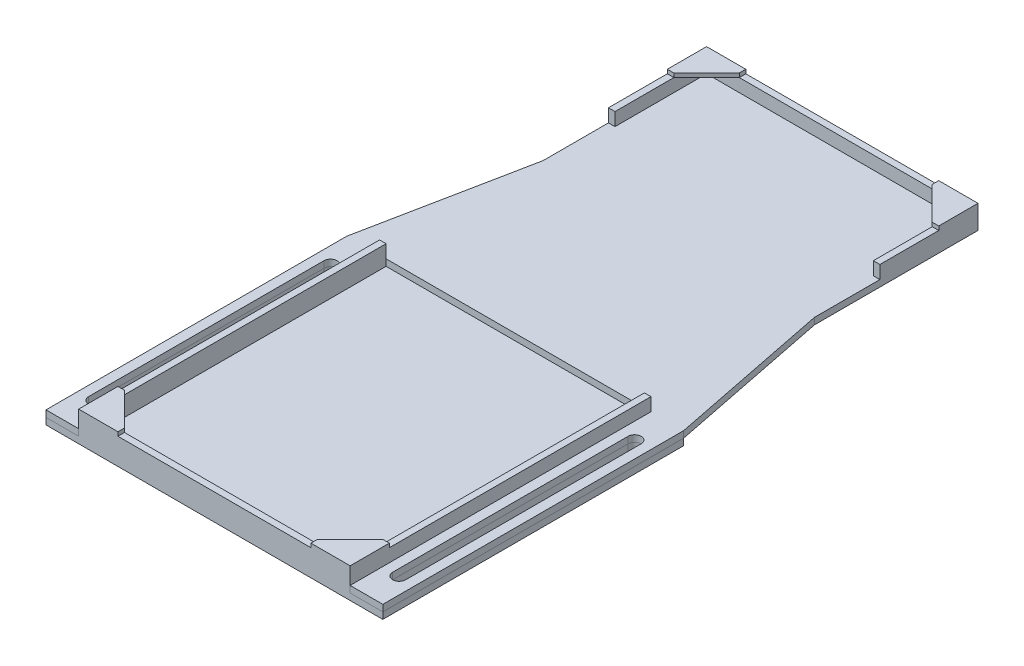
SolidWorks part; units mm, degrees
ref_plane "Alzado" through (0, 0, 0) normal (0, 0, 1) x (1, 0, 0)
ref_plane "Planta" through (0, 0, 0) normal (0, 1, 0) x (1, 0, 0)
ref_plane "Vista lateral" through (0, 0, 0) normal (1, 0, 0) x (0, 0, -1)
sketch "Croquis1" plane through (0, 0, 0) normal (0, 1, 0) x (1, 0, 0)
  line L0 (-2.3216, 1.9) -> (2.3216, 1.9) construction
  line L1 (0, 3) -> (0, -3) construction
  line L2 (3, 0) -> (-3, 0) construction
  line L3 (-2.3216, -1.9) -> (2.3216, -1.9) construction
  line L4 (2.3216, 1.9) -> (-2.3216, 1.9)
  line L5 (2.3216, -1.9) -> (-2.3216, -1.9)
  line L7 (10, -10) -> (-10, -10)
  line L8 (10, -10) -> (10, 10)
  line L9 (10, 10) -> (-10, 10)
  line L10 (-10, -10) -> (-10, 10)
  line L11 (10, -10) -> (-10, 10) construction
  line L12 (10, 10) -> (-10, -10) construction
  circle A0 centre (0, 0) radius 3
  circle A1 centre (0, 0) radius 1.9 construction
  point P11 (0, 1.9)
  dimension "D1" = 6
  dimension "D2" = 3.8
  dimension "D3" = 20
extrude "Saliente-Extruir1" add sketch "Croquis1" along normal blind 5 contours L10 L7 L8 L9 A0 | L5 A0 | L4 A0
sketch "Croquis2" plane through (0, 5, 0) normal (0, 1, 0) x (1, 0, 0)
  line L0 (-39.5, 0) -> (39.5, 0) construction
  line L1 (-10, 10) -> (-39.5, 10)
  line L6 (-39.5, 10) -> (-39.5, 0)
  line L7 (-39.5, 0) -> (-39.5, -80)
  line L8 (-39.5, -80) -> (39.5, -80)
  line L9 (0, 0) -> (0, -80) construction
  line L10 (39.5, 0) -> (39.5, -80)
  line L11 (39.5, 10) -> (39.5, 0)
  line L12 (10, 10) -> (39.5, 10)
  line L13 (-10, 10) -> (10, 10)
  point P0 (0, 0)
  point P4 (0, 0)
  dimension "D1" = 79
  dimension "D2" = 80
extrude "Saliente-Extruir2" add sketch "Croquis2" along normal blind 2
sketch "Croquis3" plane through (0, 5, 0) normal (0, -1, 0) x (1, 0, 0)
  line L0 (39.5, 80) -> (39.5, -10) construction
  line L1 (-39.5, 80) -> (39.5, 80) construction
  line L2 (-39.5, -10) -> (-39.5, 80) construction
  line L3 (39.5, 80) -> (39.5, -10)
  line L4 (-39.5, 80) -> (39.5, 80)
  line L5 (-39.5, -10) -> (-39.5, 80)
  line L11 (-41.5, -10) -> (-41.5, 82)
  line L12 (-41.5, 82) -> (41.5, 82)
  line L13 (41.5, 82) -> (41.5, -10)
  line L14 (-41.5, -10) -> (-39.5, -10)
  line L15 (41.5, -10) -> (39.5, -10)
  dimension "D1" = 2
extrude "Saliente-Extruir3" add sketch "Croquis3" against normal blind 8
sketch "Croquis4" plane through (0, 13, 0) normal (0, 1, 0) x (1, 0, 0)
  line L0 (-29.5, -80) -> (-39.5, -70)
  line L1 (39.5, -70) -> (29.5, -80)
  line L2 (-39.5, -70) -> (-39.5, -80)
  line L3 (-39.5, -80) -> (-29.5, -80)
  line L4 (39.5, -70) -> (39.5, -80)
  line L5 (39.5, -80) -> (29.5, -80)
  line L6 (-39.5, -70) -> (-41.5, -70)
  line L7 (-41.5, -82) -> (-41.5, 10) construction
  line L8 (39.5, -80) -> (-39.5, -80)
  line L9 (-39.5, -80) -> (-39.5, 10)
  line L10 (-39.5, 10) -> (-41.5, 10)
  line L11 (-41.5, 10) -> (-41.5, -82)
  line L12 (-41.5, -82) -> (41.5, -82)
  line L13 (41.5, -82) -> (41.5, 10)
  line L14 (41.5, 10) -> (39.5, 10)
  line L15 (39.5, 10) -> (39.5, -80)
  line L16 (29.5, -80) -> (-29.5, -80)
  line L24 (-29.5, -80) -> (-29.5, -82)
  line L25 (41.5, -82) -> (-41.5, -82) construction
  line L26 (39.5, -70) -> (41.5, -70)
  line L27 (41.5, 10) -> (41.5, -82) construction
  line L28 (29.5, -80) -> (29.5, -82)
  line M9 (39.5, -80) -> (-39.5, -80)
  line M10 (-39.5, -80) -> (-39.5, 10)
  line M12 (-41.5, 10) -> (-41.5, -82)
  line M13 (-41.5, -82) -> (41.5, -82)
  line M14 (41.5, -82) -> (41.5, 10)
  line M16 (39.5, 10) -> (39.5, -80)
  dimension "D1" = 0
extrude "Saliente-Extruir4" add sketch "Croquis4" along normal blind 1.2 contours L0 M9 M10 | L24 L6 M9 M10 M12 M13 | L1 M16 M9 | L28 L26 M9 M13 M14 M16
sketch "Croquis5" plane through (0, 5, 0) normal (0, -1, 0) x (1, 0, 0)
  line L0 (-41.5, 82) -> (-41.5, -10) construction
  line L1 (-41.5, 82) -> (-41.5, -10)
  line L2 (-41.5, 82) -> (-51.5, 82)
  line L3 (-51.5, 82) -> (-51.5, -10)
  line L4 (-51.5, -10) -> (-41.5, -10)
  line L5 (-46.5, 82) -> (-46.5, -10) construction
  line L6 (-46.5, 0) -> (-46.5, 72) construction
  line L7 (-48.5, 0) -> (-48.5, 72)
  line L8 (-44.5, 0) -> (-44.5, 72)
  line L9 (0, 82) -> (0, -10) construction
  line L10 (41.5, 82) -> (-41.5, 82) construction
  line L11 (10, -10) -> (-10, -10) construction
  line L12 (46.5, 0) -> (46.5, 72) construction
  line L13 (48.5, 0) -> (48.5, 72)
  line L14 (44.5, 0) -> (44.5, 72)
  line L15 (41.5, 82) -> (51.5, 82)
  line L16 (41.5, 82) -> (41.5, -10)
  line L17 (51.5, 82) -> (51.5, -10)
  line L18 (51.5, -10) -> (41.5, -10)
  arc A0 (-48.5, 0) -> (-44.5, 0) centre (-46.5, 0) ccw
  arc A1 (-44.5, 72) -> (-48.5, 72) centre (-46.5, 72) ccw
  arc A2 (48.5, 0) -> (44.5, 0) centre (46.5, 0) cw
  arc A3 (44.5, 72) -> (48.5, 72) centre (46.5, 72) cw
  point P6 (-46.5, 0)
  point P9 (-46.5, 36)
  point P22 (46.5, 36)
  dimension "D1" = 10
  dimension "D2" = 10
  dimension "D3" = 10
  dimension "D4" = 4
extrude "Saliente-Extruir5" add sketch "Croquis5" against normal blind 2
sketch "Croquis6" plane through (0, 7, 0) normal (0, 1, 0) x (1, 0, 0)
  line L4 (-48.5, -72) -> (-48.5, 0) construction
  line L5 (-44.5, 0) -> (-44.5, -72) construction
  line L6 (44.5, -72) -> (44.5, 0) construction
  line L7 (48.5, 0) -> (48.5, -72) construction
  line L8 (41.5, 10) -> (41.5, -82)
  line L9 (41.5, -82) -> (51.5, -82)
  line L10 (51.5, -82) -> (51.5, 10)
  line L11 (51.5, 10) -> (41.5, 10)
  line L12 (41.5, 10) -> (41.5, -82)
  line L13 (41.5, -82) -> (51.5, -82)
  line L14 (51.5, -82) -> (51.5, 10)
  line L15 (51.5, 10) -> (41.5, 10)
  line L16 (-51.5, -82) -> (-41.5, -82)
  line L17 (-41.5, -82) -> (-41.5, 10)
  line L18 (-41.5, 10) -> (-51.5, 10)
  line L19 (-51.5, 10) -> (-51.5, -82)
  line L20 (-51.5, -82) -> (-41.5, -82)
  line L21 (-41.5, -82) -> (-41.5, 10)
  line L22 (-41.5, 10) -> (-51.5, 10)
  line L23 (-51.5, 10) -> (-51.5, -82)
  line L24 (48.5, 0) -> (48.5, -72)
  line L25 (44.5, -72) -> (44.5, 0)
  line L26 (-44.5, 0) -> (-44.5, -72)
  line L27 (-48.5, -72) -> (-48.5, 0)
  line L28 (-41.5, 10) -> (41.5, 10)
  line L29 (-41.5, 10) -> (-41.5, 110)
  line L30 (-41.5, 110) -> (41.5, 110)
  line L31 (41.5, 110) -> (41.5, 10)
  line L32 (-51.5, 10) -> (-41.5, 60)
  line L33 (41.5, 60) -> (51.5, 10)
  arc A0 (-44.5, 0) -> (-48.5, 0) centre (-46.5, 0) ccw construction
  arc A1 (-48.5, -72) -> (-44.5, -72) centre (-46.5, -72) ccw construction
  arc A2 (44.5, -72) -> (48.5, -72) centre (46.5, -72) ccw construction
  arc A3 (48.5, 0) -> (44.5, 0) centre (46.5, 0) ccw construction
  arc A4 (48.5, 0) -> (44.5, 0) centre (46.5, 0) ccw
  arc A5 (44.5, -72) -> (48.5, -72) centre (46.5, -72) ccw
  arc A6 (-48.5, -72) -> (-44.5, -72) centre (-46.5, -72) ccw
  arc A7 (-44.5, 0) -> (-48.5, 0) centre (-46.5, 0) ccw
  arc M16 (44.5, 0) -> (48.5, 0) centre (46.5, 0) cw
  line M17 (48.5, 0) -> (48.5, -72)
  arc M18 (48.5, -72) -> (44.5, -72) centre (46.5, -72) cw
  line M19 (44.5, -72) -> (44.5, 0)
  line M20 (41.5, 10) -> (41.5, -82)
  line M21 (41.5, -82) -> (51.5, -82)
  line M22 (51.5, -82) -> (51.5, 10)
  line M23 (51.5, 10) -> (41.5, 10)
  dimension "D3" = 100
  dimension "D1" = 0
  dimension "D2" = 0
extrude "Saliente-Extruir6" add sketch "Croquis6" along normal blind 2 separate body contours L31 L30 L29 L28 | L32 L22 L29 | L33 L31 M23 | M23 M20 M21 M22 M19 M16 M17 M18 | L22 L23 L20 L21 A7 L26 A6 L27
sketch "Croquis7" plane through (0, 9, 0) normal (0, 1, 0) x (1, 0, 0)
  line L0 (-39.5, 80) -> (-39.5, 108)
  line L1 (-39.5, 108) -> (39.5, 108)
  line L2 (39.5, 108) -> (39.5, 80)
  line L3 (-41.5, 80) -> (-41.5, 110)
  line L4 (-41.5, 110) -> (41.5, 110)
  line L5 (41.5, 110) -> (41.5, 80)
  line L6 (-41.5, 80) -> (-39.5, 80)
  line L7 (39.5, 80) -> (41.5, 80)
  point P18 (0, 0)
  dimension "D1" = 2
  dimension "D2" = 30
  dimension "D3" = 30
extrude "Saliente-Extruir7" add sketch "Croquis7" along normal up to surface (4 mm away) up to face at (-40.5, 13, 30)
sketch "Croquis8" plane through (0, 13, 0) normal (0, 1, 0) x (1, 0, 0)
  line L0 (39.5, 108) -> (39.5, 80) construction
  line L1 (-39.5, 80) -> (-39.5, 108) construction
  line L6 (-39.5, 98) -> (-29.5, 108)
  line L7 (29.5, 108) -> (39.5, 98)
  line L8 (41.5, 80) -> (41.5, 110) construction
  line L9 (-41.5, 110) -> (-41.5, 80) construction
  line L10 (41.5, 110) -> (-41.5, 110) construction
  line L11 (41.5, 98) -> (41.5, 110)
  line L12 (-41.5, 110) -> (-41.5, 98)
  line L13 (41.5, 110) -> (29.5, 110)
  line L14 (29.5, 108) -> (29.5, 110)
  line L15 (39.5, 98) -> (41.5, 98)
  line L16 (-39.5, 98) -> (-41.5, 98)
  line L17 (-29.5, 108) -> (-29.5, 110)
  line L18 (-29.5, 110) -> (-41.5, 110)
extrude "Saliente-Extruir8" add sketch "Croquis8" along normal blind 1.2 contours L6 L17 L18 L12 L16 | L7 L15 L11 L13 L14
